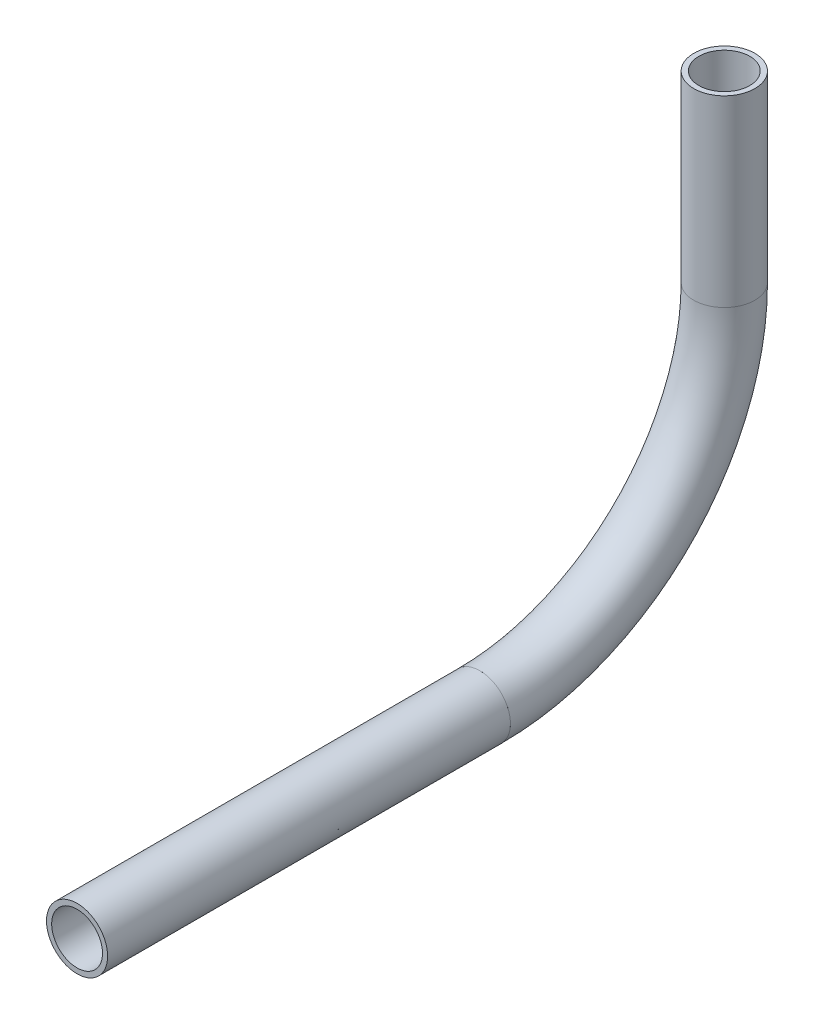
SolidWorks part; units mm, degrees
ref_plane "Front Plane" through (0, 0, 0) normal (0, 0, 1) x (1, 0, 0)
ref_plane "Top Plane" through (0, 0, 0) normal (0, 1, 0) x (1, 0, 0)
ref_plane "Right Plane" through (0, 0, 0) normal (1, 0, 0) x (0, 0, -1)
sketch "Sketch3" plane through (0, 0, 0) normal (1, 0, 0) x (0, 0, -1)
  line L0 (-259.1796, -191.1604) -> (-259.1796, -229.2604)
  line L1 (-309.9796, -280.0604) -> (-393.6907, -280.0604)
  arc A0 (-259.1796, -229.2604) -> (-309.9796, -280.0604) centre (-309.9796, -229.2604) cw
  point P2 (-405.2222, -276.7489)
  point P6 (-385.116, -278.8335)
  point P7 (-389.0036, -278.8335)
  point P8 (0, 0)
  point P9 (-393.6907, -280.0604)
  dimension "D1" = 50.8
  dimension "D2" = 38.1
other "Pipe 0.5 SCH 40(1)"
ref_plane "Plane1" through (0, -191.1604, 259.1796) normal (0, -1, 0) x (0, 0, -1)
sketch "Sketch1" plane through (0, -191.1604, 259.1796) normal (0, -1, 0) x (0, 0, -1)
  circle A0 centre (0, 0) radius 6.35
  circle A1 centre (0, 0) radius 5.2832
  point P5 (0, 0)
  dimension "In_dia" = 12.7
  dimension "Out_dia" = 10.5664
